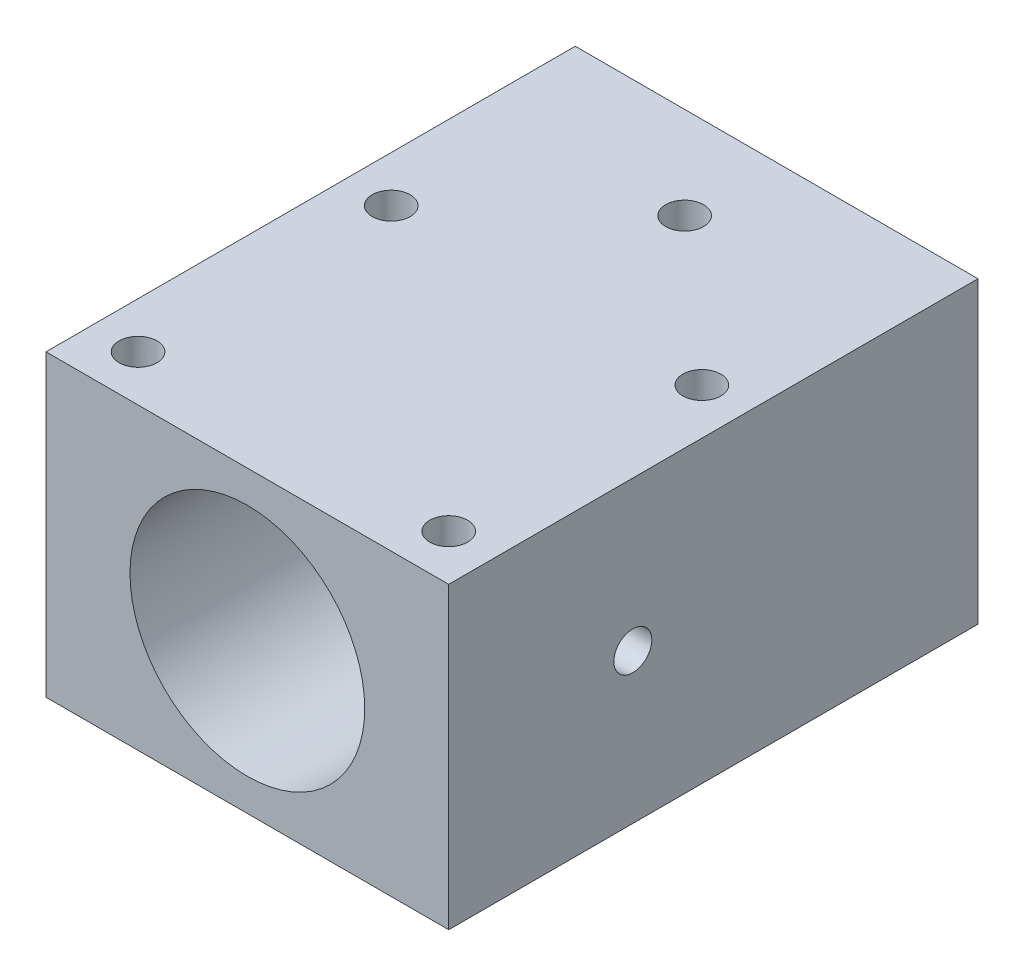
SolidWorks part; units mm, degrees
ref_plane "Front Plane" through (0, 0, 0) normal (0, 0, 1) x (1, 0, 0)
ref_plane "Top Plane" through (0, 0, 0) normal (0, 1, 0) x (1, 0, 0)
ref_plane "Right Plane" through (0, 0, 0) normal (1, 0, 0) x (0, 0, -1)
sketch "Sketch1" plane through (0, 0, 0) normal (0, 1, 0) x (1, 0, 0)
  line L1 (-17.5, -23) -> (17.5, -23)
  line L2 (-17.5, -23) -> (-17.5, 23)
  line L3 (-17.5, 23) -> (17.5, 23)
  line L4 (17.5, -23) -> (17.5, 23)
  line L5 (-17.5, -23) -> (17.5, 23) construction
  line L6 (-17.5, 23) -> (17.5, -23) construction
  point P0 (0, 0)
  dimension "D1" = 35
  dimension "D2" = 46
extrude "Boss-Extrude1" add sketch "Sketch1" along normal mid plane 26
sketch "Sketch2" plane through (0, 13, 0) normal (0, 1, 0) x (1, 0, 0)
  line L2 (0, 0) -> (-5.8518, 0) construction
  line L3 (0, 0) -> (0, -5.0733) construction
  line L6 (-17.5, -23) -> (17.5, -23) construction
  circle A0 centre (-13.5, 3) radius 1.65
  circle A6 centre (-13.5, -19) radius 1.65
  circle A7 centre (13.5, -19) radius 1.65
  circle A8 centre (13.5, 3) radius 1.65
  dimension "D1" = 3.3
  dimension "D2" = 4
  dimension "D4" = 22
  dimension "D3" = 13.5
extrude "Cut-Extrude1" cut sketch "Sketch2" against normal up to surface (26 mm away) up to face at (0, -13, 0)
sketch "Sketch5" plane through (0, 0, 23) normal (0, 0, 1) x (1, 0, 0)
  circle A0 centre (0, 0) radius 10.2
  dimension "D1" = 20.4
extrude "Cut-Extrude2" cut sketch "Sketch5" against normal up to surface (46 mm away) up to face at (0, 0, -23)
sketch "Sketch8" plane through (0, 13, 0) normal (0, 1, 0) x (1, 0, 0)
  line L0 (0, 0) -> (0, -7.5225) construction
  line L1 (17.5, 23) -> (-17.5, 23) construction
  circle A0 centre (0, 15) radius 1.65
  dimension "D1" = 3.3
  dimension "D2" = 8
extrude "Cut-Extrude3" cut sketch "Sketch8" against normal up to surface (26 mm away) up to face at (13.5, -13, -4.65)
sketch "Sketch9" plane through (-17.5, 0, 0) normal (-1, 0, 0) x (0, 0, 1)
  line L0 (0, 0) -> (-3.2448, 0) construction
  line L2 (23, 13) -> (23, -13) construction
  circle A0 centre (7, 0) radius 1.65
  dimension "D2" = 3.3
  dimension "D1" = 16
extrude "Cut-Extrude4" cut sketch "Sketch9" against normal up to surface (35 mm away) up to face at (17.5, 0, 0)
